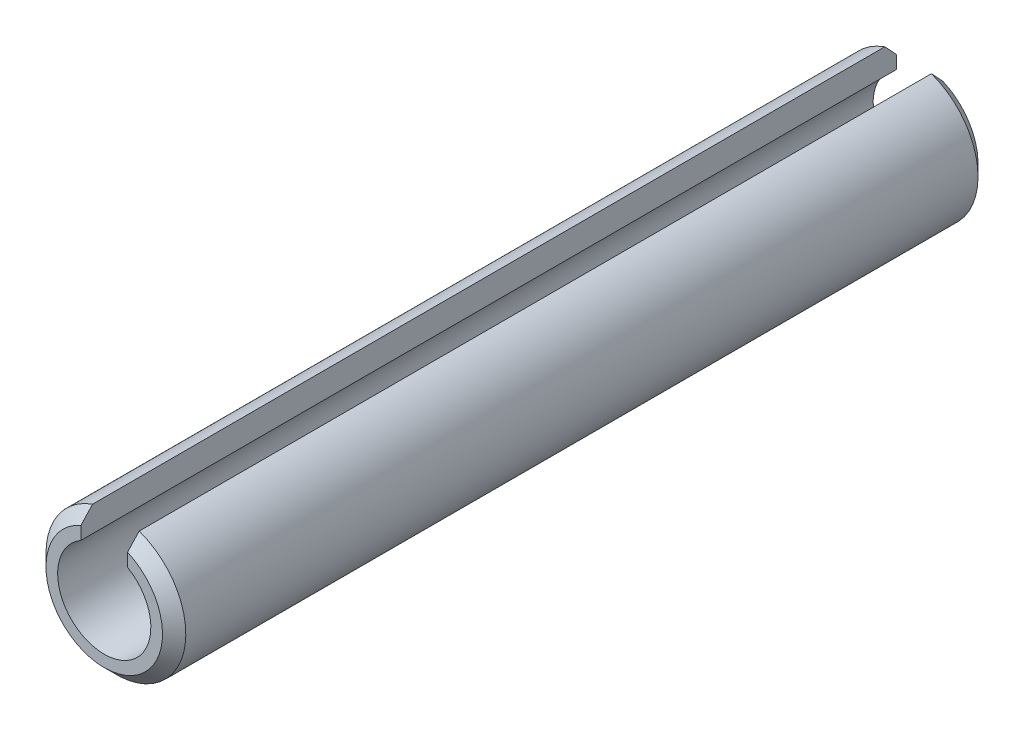
SolidWorks part; units mm, degrees
ref_plane "Plan de face" through (0, 0, 0) normal (0, 0, 1) x (1, 0, 0)
ref_plane "Plan de dessus" through (0, 0, 0) normal (0, 1, 0) x (1, 0, 0)
ref_plane "Plan de droite" through (0, 0, 0) normal (1, 0, 0) x (0, 0, -1)
sketch "Esquisse1" plane through (0, 0, 0) normal (0, 0, 1) x (1, 0, 0)
  line L0 (0, 21.956) -> (0, -27.3127) construction
  line L1 (-1, 2.8284) -> (-1, 1.7321)
  line L2 (1, 2.8284) -> (1, 1.7321)
  arc A0 (-1, 2.8284) -> (1, 2.8284) centre (0, 0) ccw
  arc A1 (-1, 1.7321) -> (1, 1.7321) centre (0, 0) ccw
  dimension "D1" = 3
  dimension "D2" = 2
  dimension "D3" = 2
extrude "Extrusion2" add sketch "Esquisse1" along normal blind 35
chamfer "Chanfrein1" distance 0.5 angle 45 2 edges at (0, -3, 0) (0, -3, 35)
